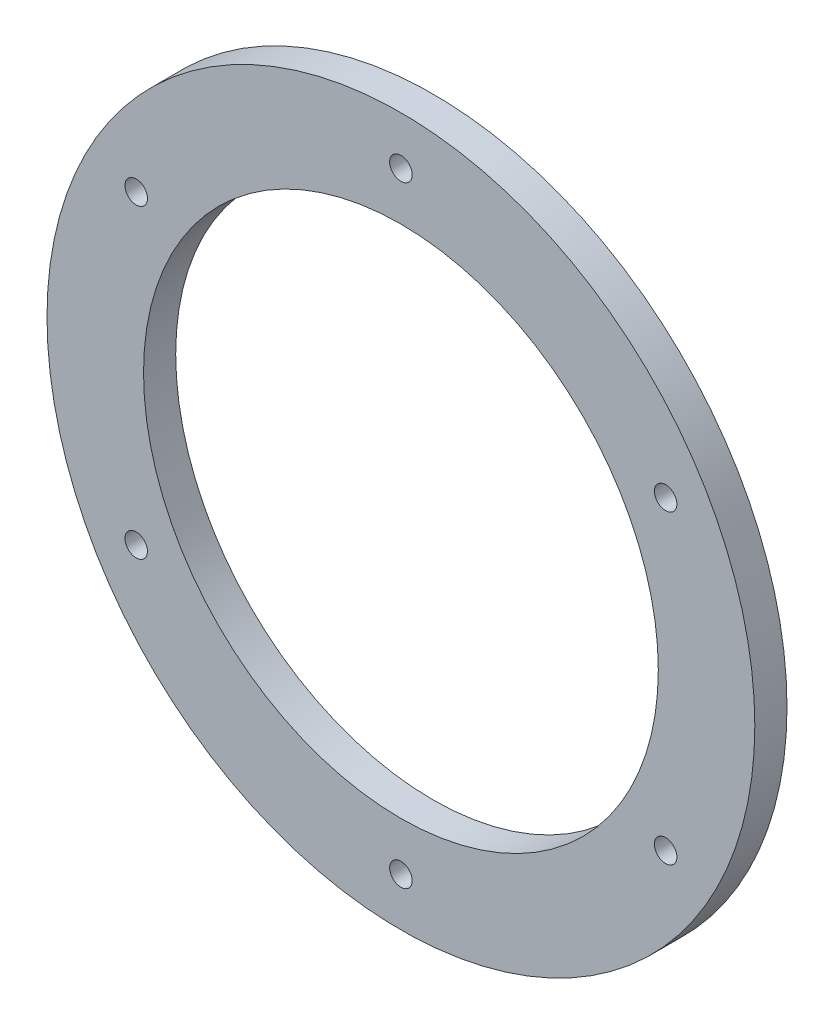
SolidWorks part; units mm, degrees
material "7075-T6 (SN)"
ref_plane "Plan de face" through (0, 0, 0) normal (0, 0, 1) x (1, 0, 0)
ref_plane "Plan de dessus" through (0, 0, 0) normal (0, 1, 0) x (1, 0, 0)
ref_plane "Plan de droite" through (0, 0, 0) normal (1, 0, 0) x (0, 0, -1)
sketch "Esquisse1" plane through (0, 0, 0) normal (0, 0, 1) x (1, 0, 0)
  line L0 (0, 47.5) -> (0, 55) construction
  line L1 (0, 47.5) -> (0, 40) construction
  circle A0 centre (0, 0) radius 55
  circle A1 centre (0, 0) radius 40
  circle A2 centre (0, 47.5) radius 1.75
  circle A3 centre (41.1362, 23.75) radius 1.75
  circle A4 centre (41.1362, -23.75) radius 1.75
  circle A5 centre (0, -47.5) radius 1.75
  circle A6 centre (-41.1362, -23.75) radius 1.75
  circle A7 centre (-41.1362, 23.75) radius 1.75
  point P20 (0, 0)
  dimension "D1" = 80
  dimension "D2" = 110
  dimension "D3" = 3.5
  dimension "D4" = 6
extrude "Boss.-Extru.1" add sketch "Esquisse1" along normal blind 5
